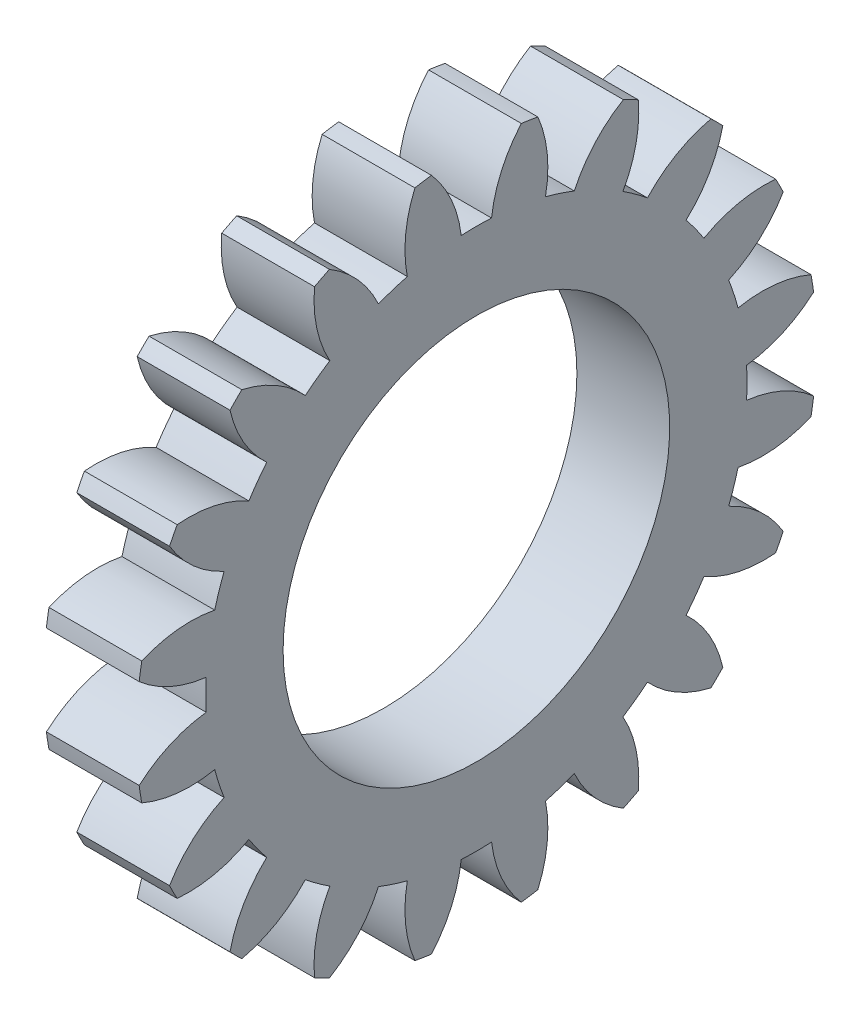
SolidWorks part; units mm, degrees
ref_plane "Plane1" through (0, 0, 0) normal (0, 0, 1) x (1, 0, 0)
ref_plane "Plane2" through (0, 0, 0) normal (0, 1, 0) x (1, 0, 0)
ref_plane "Plane3" through (0, 0, 0) normal (1, 0, 0) x (0, 0, -1)
sketch "HoldingSke" plane through (0, 0, 0) normal (0, 1, 0) x (1, 0, 0)
  line L0 (0, 0) -> (0.2349, -0.0855)
  line L1 (-15, 0) -> (100, 0) construction
  line L2 (0, 0) -> (-2.1039, 2.3779)
  line L3 (0, 0) -> (-11.863, 4.5341)
  line L4 (0, 0) -> (8.1152, 2.9537)
  line L5 (0, 0) -> (-46.8476, -17.4728)
  line L6 (0, 0) -> (-9.9476, -6.7116)
  line L7 (-2.1039, 2.3779) -> (8.6586, 51.2059)
  line L8 (-76.2, 54.61) -> (-71.9, 54.61)
  line L9 (-71.009, 38.7566) -> (-53.1078, 45.2721)
  line L10 (-76.2, 71.12) -> (104.1128, 71.12)
  line L11 (0, 0) -> (-12, 0)
  line L12 (-76.2, 101.6) -> (-76.073, 101.6)
  line L13 (24.9733, 27.94) -> (52.9518, 28.4284)
  line L14 (24.9733, 27.94) -> (24.9743, 27.94)
  line L15 (24.9733, 27.94) -> (100.4006, 29.5858)
  line L16 (-63.627, -4) -> (-12.827, -4)
  circle A0 centre (0, 0) radius 25
  circle A1 centre (0, 0) radius 34.999
  circle A2 centre (0, 0) radius 37.5
  circle A3 centre (0, 0) radius 25
  dimension "Hub_dia" = 75
  dimension "Overall_len" = 50
  dimension "Thickness" = 12
  dimension "OAL" = 50.0001
  dimension "Ap" = 20
  dimension "H" = 19.05
  dimension "Pitch_radius" = 180.3128
  dimension "Width" = 12
  dimension "Addendum_fac" = 1
  dimension "Dedendum_fac" = 1.25
  dimension "Clearance_fac" = 0.25
  dimension "Dedendum_add" = 0.001
sketch "BasProSke" plane through (0, 0, 0) normal (0, 1, 0) x (1, 0, 0)
  line L0 (-10, 0) -> (60, 0) construction
  line L1 (0, 0) -> (0, 44)
  line L2 (0, 0) -> (12, 0)
  line L3 (12, 0) -> (12, 44)
  line L4 (12, 44) -> (0, 44)
  dimension "Thickness" = 12
revolve "Base-Revolve" add sketch "BasProSke" angle 360 about L0
sketch "TooCutSke" plane through (0, 0, 0) normal (1, 0, 0) x (0, 0, -1)
  line L1 (0, 0) -> (0, 107) construction
  line L2 (0, 0) -> (-3.3605, 39.8586) construction
  line L3 (0, 0) -> (-12.4815, 78.8048) construction
  line L4 (-3.3605, 39.8586) -> (-6.2407, 39.4024) construction
  arc A0 (1.9617, 34.944) -> (-1.9617, 34.944) centre (0, 0) ccw
  arc A1 (5.8321, 43.6374) -> (-5.8321, 43.6374) centre (0, 0) ccw
  circle A2 centre (0, 0) radius 40 construction
  circle A3 centre (0, 0) radius 37.5877 construction
  arc A4 (-1.9617, 34.944) -> (-5.8321, 43.6374) centre (-17.8525, 33.0775) ccw
  arc A5 (5.8321, 43.6374) -> (1.9617, 34.944) centre (17.8525, 33.0775) ccw
extrude "ToothCut" cut sketch "TooCutSke" along normal through all
fillet "Breaks" [suppressed] radius 0.08
fillet "RootFillets" [suppressed] radius 1.001
pattern_circular "TeethCuts" count 20 every 18 about axis through (-10, 0, 0) along (1, 0, 0) of "ToothCut", "RootFillets", "Breaks"
sketch "HubNeaOneSke" plane through (0, 0, 0) normal (-1, 0, 0) x (0, 0, 1)
  circle A0 centre (0, 0) radius 34.999
extrude "HubNearOne" [suppressed] add sketch "HubNeaOneSke" along normal blind 38.0001
sketch "HubNeaBotSke" plane through (0, 0, 0) normal (-1, 0, 0) x (0, 0, 1)
  circle A0 centre (0, 0) radius 34.999
extrude "HubNearBoth" [suppressed] add sketch "HubNeaBotSke" along normal blind 19
ref_plane "FarPln" through (12, 0, 0) normal (1, 0, 0) x (0, 0, -1)
sketch "HubFarSke" plane through (12, 0, 0) normal (1, 0, 0) x (0, 0, -1)
  circle A0 centre (0, 0) radius 34.999
extrude "HubFar" [suppressed] add sketch "HubFarSke" along normal blind 19
sketch "BorSke" plane through (0, 0, 0) normal (1, 0, 0) x (0, 0, -1)
  circle A0 centre (0, 0) radius 25
extrude "Bore" cut sketch "BorSke" along normal mid plane 100.0001
sketch "KeySke" plane through (0, 0, 0) normal (1, 0, 0) x (0, 0, -1)
  line L0 (-8, 0) -> (-8, 29.3)
  line L1 (-8, 29.3) -> (8, 29.3)
  line L2 (8, 29.3) -> (8, 0)
  line L3 (0, 0) -> (0, 34) construction
  line L4 (-8, 0) -> (8, 0)
extrude "Keyway" [suppressed] cut sketch "KeySke" along normal mid plane 100.0001
pattern_circular "Keyway2" [suppressed] count 2 every 90 about axis through (-10, 0, 0) along (1, 0, 0)
equation "' \"Module@HoldingSke\" = 6.35"
equation "' \"Num_teeth@HoldingSke\" = 12"
equation "' \"Ap@HoldingSke\" =  20"
equation "' \"Ap@HoldingSke\" = 20"
equation "' \"Width@HoldingSke\" = 0.5 * 25.4"
equation "' \"Hub_dia@HoldingSke\"= 1 * 25.4"
equation "' \"Hub_dia@HoldingSke\" = 1 * 25.4"
equation "' \"Overall_len@HoldingSke\" = 1.0 * 25.4"
equation "' \"Bore@HoldingSke\" = 0.75 * 25.4"
equation "' \"T_dim@HoldingSke\" = 0.1 * 25.4"
equation "' \"Width@KeySke\" = 0.25 * 25.4"
equation "' \"Show_teeth@HoldingSke\" = 13"
equation "' \"Backlash@HoldingSke\" = 0.009 * 25.4"
equation "' \"Addendum_fac@HoldingSke\" = 1.0"
equation "' \"Dedendum_fac@HoldingSke\" = 1.25"
equation "' \"Dedendum_add@HoldingSke\" = 0.00005 * 25.4"
equation "' \"Clearance_fac@HoldingSke\" = 0.25"
equation "\"Pitch@HoldingSke\" = 1 / \"Module@HoldingSke\""
equation "\"Overcut_dia@TooCutSke\" = (\"Num_teeth@HoldingSke\" + 2 * \"Addendum_fac@HoldingSke\") / \"Pitch@HoldingSke\" + 0.002 * 25.4"
equation "\"Pitch_dia@TooCutSke\" = \"Num_teeth@HoldingSke\" / \"Pitch@HoldingSke\""
equation "\"Base_dia@TooCutSke\" = \"Num_teeth@HoldingSke\" / \"Pitch@HoldingSke\" * cos((\"Ap@HoldingSke\"  * 3.14159265 / 180))"
equation "\"Root_dia@TooCutSke\" = (\"Num_teeth@HoldingSke\" + 2) / \"Pitch@HoldingSke\" - 2 * (\"Addendum_fac@HoldingSke\" + \"Dedendum_fac@HoldingSke\") / \"Pitch@HoldingSke\" - \"Dedendum_add@HoldingSke\" * 2"
equation "\"Half_ang@TooCutSke\" = 180 / \"Num_teeth@HoldingSke\""
equation "\"Half_CT@TooCutSke\" = \"Num_teeth@HoldingSke\" / \"Pitch@HoldingSke\" * sin((3.14159265 / 2 / \"Num_teeth@HoldingSke\")) / 2 - 7 * \"Backlash@HoldingSke\" / 4"
equation "\"Flank_rad@TooCutSke\" = \"Num_teeth@HoldingSke\" / \"Pitch@HoldingSke\" / 5"
equation "\"Radius@RootFillets\" = \"Clearance_fac@HoldingSke\" / \"Pitch@HoldingSke\" + \"Dedendum_add@HoldingSke\""
equation "\"Break_rad@Breaks\" = 0.02 / \"Pitch@HoldingSke\""
equation "\"Thickness@HoldingSke\" = \"Width@HoldingSke\""
equation "\"OAL@HoldingSke\" = \"Thickness@HoldingSke\""
equation "\"MHD@HoldingSke\" = (\"Num_teeth@HoldingSke\" + 2) / \"Pitch@HoldingSke\" - 2 * (\"Addendum_fac@HoldingSke\" + \"Dedendum_fac@HoldingSke\")  / \"Pitch@HoldingSke\" - \"Dedendum_add@HoldingSke\" * 2"
equation "\"MBD@HoldingSke\" = (\"Num_teeth@HoldingSke\" + 2) / \"Pitch@HoldingSke\" - 2 * (\"Addendum_fac@HoldingSke\" + \"Dedendum_fac@HoldingSke\")  / \"Pitch@HoldingSke\" - \"Dedendum_add@HoldingSke\" * 2 - 0.002 * 25.4"
equation "\"MHD@HoldingSke\" = ((sgn( \"MHD@HoldingSke\" - \"Hub_dia@HoldingSke\" )-1)*( \"MHD@HoldingSke\" - \"Hub_dia@HoldingSke\" ))/-2+ \"Hub_dia@HoldingSke\""
equation "\"MBD@HoldingSke\" = ((sgn( \"MBD@HoldingSke\" - \"Bore@HoldingSke\" )-1)*( \"MBD@HoldingSke\" - \"Bore@HoldingSke\" ))/-2+ \"Bore@HoldingSke\""
equation "\"OAL@HoldingSke\" = ((sgn( \"OAL@HoldingSke\" - \"Overall_len@HoldingSke\" )+1)*( \"OAL@HoldingSke\" - \"Overall_len@HoldingSke\" ))/2 + \"Overall_len@HoldingSke\" + 0.000002 * 25.4"
equation "\"Num_teeth@TeethCuts\" = int( \"Show_teeth@HoldingSke\" ) + 1"
equation "\"Num_teeth@TeethCuts\" = ((sgn( \"Num_teeth@TeethCuts\" - \"Num_teeth@HoldingSke\" )-1)*( \"Num_teeth@TeethCuts\" - \"Num_teeth@HoldingSke\" ))/-2+ \"Num_teeth@HoldingSke\""
equation "\"Num_teeth@TeethCuts\" = ((sgn( \"Num_teeth@TeethCuts\" - 2.0)+1)*( \"Num_teeth@TeethCuts\" - 2.0))/2 +2.0"
equation "\"Angle@TeethCuts\" = 360.0 / \"Num_teeth@HoldingSke\""
equation "\"Diameter@BasProSke\" = (\"Num_teeth@HoldingSke\" + 2 * \"Addendum_fac@HoldingSke\") / \"Pitch@HoldingSke\""
equation "\"Thickness@BasProSke\"  = \"Thickness@HoldingSke\""
equation "' \"Fillet_rad@BasProSke\" =  \"Thickness@HoldingSke\" * 0.05"
equation "' \"Fillet_rad@BasProSke\" = \"Thickness@HoldingSke\" * 0.05"
equation "\"MHD@HoldingSke\" = ((sgn( \"MHD@HoldingSke\" - \"Root_dia@TooCutSke\" )-1)*( \"MHD@HoldingSke\" - \"Root_dia@TooCutSke\" ))/-2+ \"Root_dia@TooCutSke\""
equation "\"Diameter@HubNeaOneSke\" = \"MHD@HoldingSke\""
equation "\"Length@HubNearOne\" = \"OAL@HoldingSke\" - \"Thickness@BasProSke\""
equation "\"Diameter@HubNeaBotSke\" = \"MHD@HoldingSke\""
equation "\"Length@HubNearBoth\" = ( \"OAL@HoldingSke\" - \"Thickness@BasProSke\" ) / 2.0"
equation "\"Thickness@FarPln\" = \"Thickness@BasProSke\""
equation "\"Diameter@HubFarSke\" = \"MHD@HoldingSke\""
equation "\"Length@HubFar\" = ( \"OAL@HoldingSke\" - \"Thickness@BasProSke\" ) / 2.0"
equation "\"Diameter@BorSke\" = \"MBD@HoldingSke\""
equation "\"D1@Bore\" = \"OAL@HoldingSke\" * 2.0"
equation "\"D1@Keyway\" = \"OAL@HoldingSke\" * 2.0"
equation "\"Offset@KeySke\" = \"T_dim@HoldingSke\" + \"MBD@HoldingSke\" / 2.0"
